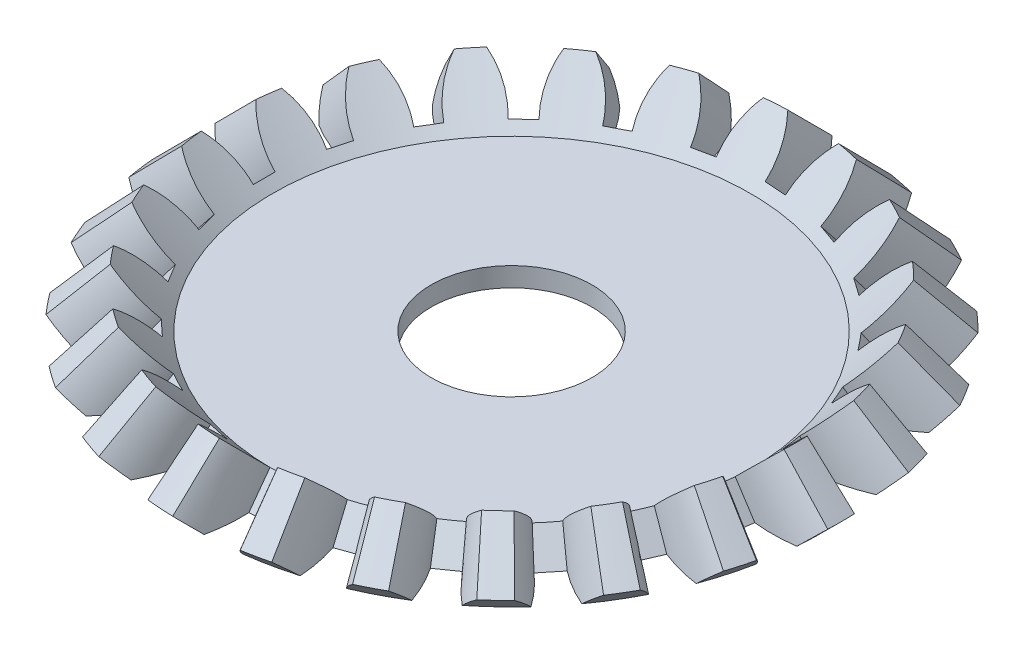
SolidWorks part; units mm, degrees
ref_plane "Front Plane" through (0, 0, 0) normal (0, 0, 1) x (1, 0, 0)
ref_plane "Top Plane" through (0, 0, 0) normal (0, 1, 0) x (1, 0, 0)
ref_plane "Right Plane" through (0, 0, 0) normal (1, 0, 0) x (0, 0, -1)
sketch "Sketch1" plane through (0, 0, 0) normal (1, 0, 0) x (0, 0, -1)
  line L0 (0, 209.8707) -> (0, -180.9373) construction
  line L1 (0, 0) -> (0, 1.2)
  line L2 (0, 1.2) -> (-14.8431, 1.2)
  line L3 (-14.8431, 1.2) -> (-17.6716, 4.0284)
  line L4 (-17.6716, 4.0284) -> (-20.5, 1.2)
  line L5 (-20.5, 1.2) -> (-19.3, 0)
  line L6 (-19.3, 0) -> (0, 0)
  dimension "D1" = 1.2
  dimension "D2" = 2.8284
  dimension "D4" = 45
  dimension "D6" = 17.6716
revolve "Revolve1" add sketch "Sketch1" angle 360 about L0
sketch "Sketch2" plane through (0, 0, 0) normal (0, 0, 1) x (1, 0, 0)
  line L0 (0, -14.2123) -> (0, 21.7) construction
  line L1 (0, 21.7) -> (-28.4878, -6.7878) construction
  line L2 (-17.6716, 4.0284) -> (-20.5, 1.2) construction
ref_plane "Plane1" through (-9.65, -9.65, 0) normal (-0.7071, -0.7071, 0) x (-0.7071, 0.7071, 0)
sketch "Sketch3" plane through (-9.65, -9.65, 0) normal (-0.7071, -0.7071, 0) x (-0.7071, 0.7071, 0)
  line L0 (11.5859, -0.7883) -> (11.5859, 0.7883)
  line L1 (15.3775, 2.0451) -> (15.3775, -2.0451)
  line L2 (15.3775, 0) -> (11.5859, 0) construction
  arc A0 (11.5859, 0.7883) -> (15.3775, 2.0451) centre (11.5859, 7.1362) ccw
  arc A1 (11.5859, -0.7883) -> (15.3775, -2.0451) centre (11.5859, -7.1362) cw
  point P10 (11.5859, -0.7883)
  point P13 (11.5859, 0.7883)
sketch "Sketch4" plane through (0, 0, 0) normal (0, 0, 1) x (1, 0, 0)
  point P0 (0, 21.7)
loft "Cut-Loft1" cut profiles "Sketch4", "Sketch3"
pattern_circular "CirPattern1" count 23 over 360 about axis through (0, 0, 0) along (0, 1, 0) of "Cut-Loft1"
sketch "Sketch5" plane through (0, 1.2, 0) normal (0, 1, 0) x (1, 0, 0)
  circle A0 centre (0, 0) radius 5
extrude "Cut-Extrude1" cut sketch "Sketch5" against normal blind 1.2
